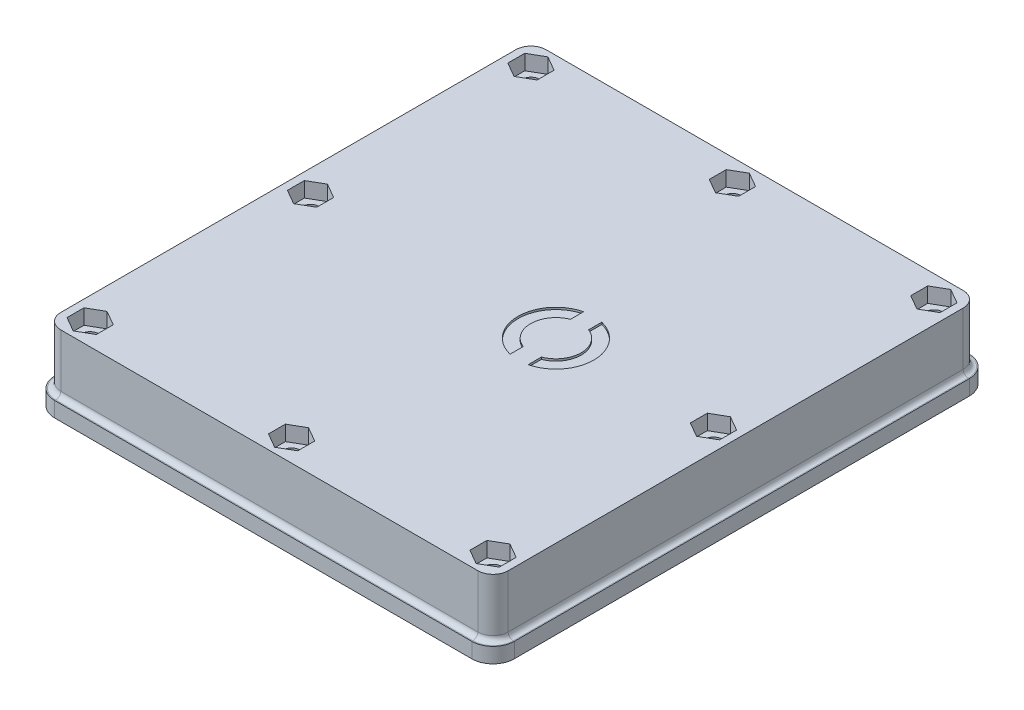
SolidWorks part; units mm, degrees
ref_plane "Спереди" through (0, 0, 0) normal (0, 0, 1) x (1, 0, 0)
ref_plane "Сверху" through (0, 0, 0) normal (0, 1, 0) x (1, 0, 0)
ref_plane "Справа" through (0, 0, 0) normal (1, 0, 0) x (0, 0, -1)
sketch "Эскиз1" plane through (0, 0, 0) normal (0, 1, 0) x (1, 0, 0)
  line L0 (-41.9993, -47.5511) -> (40.5007, -47.5511)
  line L1 (43.5007, 45.4489) -> (43.5007, -44.5511)
  line L2 (-44.9993, 45.4489) -> (-44.9993, -44.5511)
  line L3 (-41.9993, 48.4489) -> (40.5007, 48.4489)
  line L4 (-17.4039, -31.5511) -> (-17.4039, -29.173)
  line L5 (-17.4039, -29.173) -> (-15.9993, -29.173)
  line L6 (-15.9993, 40.4489) -> (38.0007, 40.4489)
  line L7 (38.0007, 10.4489) -> (38.0007, 40.4489)
  line L8 (35.5007, 10.4489) -> (38.0007, 10.4489)
  line L9 (35.5007, 10.4489) -> (35.5007, -29.0511)
  line L10 (35.5007, -39.5511) -> (35.5007, -30.0511)
  line L11 (27.5007, -39.5511) -> (35.5007, -39.5511)
  line L12 (27.5007, -30.0511) -> (27.5007, -39.5511)
  line L13 (21.0007, -30.0511) -> (27.5007, -30.0511)
  line L14 (-15.9993, -29.173) -> (-15.9993, -31.5511)
  line L15 (-15.9993, -31.5511) -> (21.0007, -31.5511)
  line L17 (-17.4039, 40.4489) -> (-17.4039, 31.327)
  line L18 (-17.4039, 40.4489) -> (-17.4039, 41.327)
  line L19 (-17.4039, 31.327) -> (-15.9993, 31.327)
  line L20 (-15.9993, 31.327) -> (-15.9993, 40.4489)
  line L25 (21.0007, -31.5511) -> (21.0007, -30.0511)
  line L26 (35.5007, -29.0511) -> (35.5007, -30.0511)
  line L27 (-36.6539, 1.077) -> (-17.6539, 1.077) construction
  line L29 (-17.4039, -39.173) -> (-36.9039, -39.173)
  line L30 (-17.4039, -39.173) -> (-17.4039, -31.5511)
  line L31 (-17.4039, 41.327) -> (-36.9039, 41.327)
  line L32 (-36.9039, -39.173) -> (-36.9039, 41.327)
  line L33 (-17.4039, -39.173) -> (-36.9039, 41.327) construction
  line L34 (-17.4039, 41.327) -> (-36.9039, -39.173) construction
  circle A0 centre (-40.5993, 0.4489) radius 1.7
  arc A1 (-44.9993, -44.5511) -> (-41.9993, -47.5511) centre (-41.9993, -44.5511) ccw
  circle A2 centre (-40.5993, -43.1511) radius 1.7
  circle A3 centre (-0.7493, -43.1511) radius 1.7
  arc A4 (40.5007, -47.5511) -> (43.5007, -44.5511) centre (40.5007, -44.5511) ccw
  circle A5 centre (39.1007, -43.1511) radius 1.7
  circle A6 centre (39.1007, 0.4489) radius 1.7
  arc A7 (43.5007, 45.4489) -> (40.5007, 48.4489) centre (40.5007, 45.4489) ccw
  circle A8 centre (39.1007, 44.0489) radius 1.7
  circle A9 centre (-0.7493, 44.0489) radius 1.7
  circle A10 centre (-40.5993, 44.0489) radius 1.7
  arc A11 (-41.9993, 48.4489) -> (-44.9993, 45.4489) centre (-41.9993, 45.4489) ccw
  point P20 (-27.1539, 1.077)
  point P60 (-27.1539, 41.327)
  point P61 (-27.1539, -39.173)
  dimension "D3" = 10
  dimension "D1" = 19.5
  dimension "D2" = 80.5
  dimension "D4" = 10
extrude "Бобышка-Вытянуть1" add sketch "Эскиз1" along normal blind 10
sketch "Эскиз2" plane through (0, 10, 0) normal (0, 1, 0) x (1, 0, 0)
  line L0 (43.5007, 45.4489) -> (43.5007, -44.5511) construction
  line L1 (-41.9993, -47.5511) -> (40.5007, -47.5511) construction
  line L2 (-44.9993, 45.4489) -> (-44.9993, -44.5511) construction
  line L3 (-41.9993, 48.4489) -> (40.5007, 48.4489) construction
  line L4 (43.5007, 45.4489) -> (43.5007, -44.5511)
  line L5 (-41.9993, -47.5511) -> (40.5007, -47.5511)
  line L6 (-44.9993, 45.4489) -> (-44.9993, -44.5511)
  line L7 (-41.9993, 48.4489) -> (40.5007, 48.4489)
  arc A0 (43.5007, 45.4489) -> (40.5007, 48.4489) centre (40.5007, 45.4489) ccw construction
  arc A1 (40.5007, -47.5511) -> (43.5007, -44.5511) centre (40.5007, -44.5511) ccw construction
  arc A2 (-44.9993, -44.5511) -> (-41.9993, -47.5511) centre (-41.9993, -44.5511) ccw construction
  arc A3 (-41.9993, 48.4489) -> (-44.9993, 45.4489) centre (-41.9993, 45.4489) ccw construction
  arc A4 (43.5007, 45.4489) -> (40.5007, 48.4489) centre (40.5007, 45.4489) ccw
  arc A5 (40.5007, -47.5511) -> (43.5007, -44.5511) centre (40.5007, -44.5511) ccw
  arc A6 (-44.9993, -44.5511) -> (-41.9993, -47.5511) centre (-41.9993, -44.5511) ccw
  arc A7 (-41.9993, 48.4489) -> (-44.9993, 45.4489) centre (-41.9993, 45.4489) ccw
  circle A8 centre (39.1007, 0.4489) radius 1.7 construction
  circle A9 centre (39.1007, -43.1511) radius 1.7 construction
  circle A10 centre (-0.7493, -43.1511) radius 1.7 construction
  circle A11 centre (-40.5993, -43.1511) radius 1.7 construction
  circle A12 centre (-40.5993, 0.4489) radius 1.7 construction
  circle A13 centre (39.1007, 44.0489) radius 1.7 construction
  circle A14 centre (-0.7493, 44.0489) radius 1.7 construction
  circle A15 centre (-40.5993, 44.0489) radius 1.7 construction
  circle A16 centre (39.1007, 0.4489) radius 1.7
  circle A17 centre (39.1007, -43.1511) radius 1.7
  circle A18 centre (-0.7493, -43.1511) radius 1.7
  circle A19 centre (-40.5993, -43.1511) radius 1.7
  circle A20 centre (-40.5993, 0.4489) radius 1.7
  circle A21 centre (39.1007, 44.0489) radius 1.7
  circle A22 centre (-0.7493, 44.0489) radius 1.7
  circle A23 centre (-40.5993, 44.0489) radius 1.7
extrude "Бобышка-Вытянуть2" add sketch "Эскиз2" along normal blind 2.5
fillet "Скругление1" radius 9.5 1 edges at (-36.9039, 10, -1.077)
fillet "Скругление2" radius 9.5 1 edges at (-17.4039, 10, 34.173)
sketch "Эскиз3" plane through (0, 10, 0) normal (0, -1, 0) x (1, 0, 0)
  line L0 (39.1007, -0.4489) -> (-40.5993, -0.4489) construction
  circle A0 centre (9.1007, -2.4489) radius 3
  circle A1 centre (9.1007, -2.4489) radius 5
  point P4 (9.1007, -2.4489)
  dimension "D3" = 6
  dimension "D4" = 10
  dimension "D1" = 2
  dimension "D2" = 30
fillet "Скругление3" radius 9.5 1 edges at (-17.4039, 10, -36.327)
extrude "Бобышка-Вытянуть3" add sketch "Эскиз3" along normal blind 3
sketch "Эскиз4" plane through (0, 12.5, 0) normal (0, 1, 0) x (1, 0, 0)
  line L0 (8.3881, 12.0563) -> (8.3881, -12.8952) construction
  line L1 (6.5927, 7.2819) -> (6.5927, 4.6666)
  line L2 (10.1834, 7.2819) -> (10.1834, 4.6666)
  line L3 (6.5927, -4.6666) -> (6.5927, -7.2819)
  line L4 (10.1834, -4.6666) -> (10.1834, -7.2819)
  arc A0 (6.5927, 4.6666) -> (6.5927, -4.6666) centre (8.3881, 0) ccw
  arc A1 (6.5927, 7.2819) -> (6.5927, -7.2819) centre (8.3881, 0) ccw
  arc A2 (10.1834, -4.6666) -> (10.1834, 4.6666) centre (8.3881, 0) ccw
  arc A3 (10.1834, -7.2819) -> (10.1834, 7.2819) centre (8.3881, 0) ccw
  dimension "D1" = 10
  dimension "D2" = 15
extrude "Вырез-Вытянуть1" cut sketch "Эскиз4" against normal blind 0.4
sketch "Эскиз5" plane through (0, 12.5, 0) normal (0, 1, 0) x (1, 0, 0)
  line L0 (43.5007, 0.4489) -> (-44.9993, 0.4489) construction
  line L1 (-40.5993, 40.7002) -> (-37.6993, 42.3746)
  line L2 (-37.6993, 42.3746) -> (-37.6993, 45.7232)
  line L3 (-37.6993, 45.7232) -> (-40.5993, 47.3975)
  line L4 (-40.5993, 47.3975) -> (-43.4993, 45.7232)
  line L5 (-43.4993, 45.7232) -> (-43.4993, 42.3746)
  line L6 (-43.4993, 42.3746) -> (-40.5993, 40.7002)
  line L7 (-0.7493, 40.7002) -> (2.1507, 42.3746)
  line L8 (2.1507, 42.3746) -> (2.1507, 45.7232)
  line L9 (2.1507, 45.7232) -> (-0.7493, 47.3975)
  line L10 (-0.7493, 47.3975) -> (-3.6493, 45.7232)
  line L11 (-3.6493, 45.7232) -> (-3.6493, 42.3746)
  line L12 (-3.6493, 42.3746) -> (-0.7493, 40.7002)
  line L13 (-40.5993, 3.7975) -> (-43.4993, 2.1232)
  line L14 (-43.4993, 2.1232) -> (-43.4993, -1.2254)
  line L15 (-43.4993, -1.2254) -> (-40.5993, -2.8998)
  line L16 (-40.5993, -2.8998) -> (-37.6993, -1.2254)
  line L17 (-37.6993, -1.2254) -> (-37.6993, 2.1232)
  line L18 (-37.6993, 2.1232) -> (-40.5993, 3.7975)
  line L19 (43.5007, -44.5511) -> (43.5007, 45.4489) construction
  line L20 (-44.9993, 45.4489) -> (-44.9993, -44.5511) construction
  line L21 (-0.7493, 48.4489) -> (-0.7493, -47.5511) construction
  line L22 (40.5007, 48.4489) -> (-41.9993, 48.4489) construction
  line L23 (-41.9993, -47.5511) -> (40.5007, -47.5511) construction
  line L24 (36.2007, 2.1232) -> (39.1007, 3.7975)
  line L25 (36.2007, -1.2254) -> (36.2007, 2.1232)
  line L26 (39.1007, -2.8998) -> (36.2007, -1.2254)
  line L27 (42.0007, -1.2254) -> (39.1007, -2.8998)
  line L28 (42.0007, 2.1232) -> (42.0007, -1.2254)
  line L29 (39.1007, 3.7975) -> (42.0007, 2.1232)
  line L30 (42.0007, 42.3746) -> (39.1007, 40.7002)
  line L31 (42.0007, 45.7232) -> (42.0007, 42.3746)
  line L32 (39.1007, 47.3975) -> (42.0007, 45.7232)
  line L33 (36.2007, 45.7232) -> (39.1007, 47.3975)
  line L34 (36.2007, 42.3746) -> (36.2007, 45.7232)
  line L35 (39.1007, 40.7002) -> (36.2007, 42.3746)
  line L36 (39.1007, -39.8025) -> (36.2007, -41.4768)
  line L37 (36.2007, -41.4768) -> (36.2007, -44.8254)
  line L38 (36.2007, -44.8254) -> (39.1007, -46.4998)
  line L39 (39.1007, -46.4998) -> (42.0007, -44.8254)
  line L40 (42.0007, -44.8254) -> (42.0007, -41.4768)
  line L41 (42.0007, -41.4768) -> (39.1007, -39.8025)
  line L42 (-3.6493, -41.4768) -> (-0.7493, -39.8025)
  line L43 (-3.6493, -44.8254) -> (-3.6493, -41.4768)
  line L44 (-0.7493, -46.4998) -> (-3.6493, -44.8254)
  line L45 (2.1507, -44.8254) -> (-0.7493, -46.4998)
  line L46 (2.1507, -41.4768) -> (2.1507, -44.8254)
  line L47 (-0.7493, -39.8025) -> (2.1507, -41.4768)
  line L48 (-43.4993, -41.4768) -> (-40.5993, -39.8025)
  line L49 (-43.4993, -44.8254) -> (-43.4993, -41.4768)
  line L50 (-40.5993, -46.4998) -> (-43.4993, -44.8254)
  line L51 (-37.6993, -44.8254) -> (-40.5993, -46.4998)
  line L52 (-37.6993, -41.4768) -> (-37.6993, -44.8254)
  line L53 (-40.5993, -39.8025) -> (-37.6993, -41.4768)
  circle A0 centre (-40.5993, 44.0489) radius 2.9 construction
  circle A1 centre (-0.7493, 44.0489) radius 2.9 construction
  circle A2 centre (-40.5993, 0.4489) radius 2.9 construction
  circle A3 centre (39.1007, 0.4489) radius 2.9 construction
  circle A4 centre (39.1007, 44.0489) radius 2.9 construction
  circle A5 centre (39.1007, -43.1511) radius 2.9 construction
  circle A6 centre (-0.7493, -43.1511) radius 2.9 construction
  circle A7 centre (-40.5993, -43.1511) radius 2.9 construction
extrude "Вырез-Вытянуть2" cut sketch "Эскиз5" against normal blind 3
sketch "Эскиз6" plane through (0, 10, 0) normal (0, -1, 0) x (1, 0, 0)
  line L0 (27.5007, 30.0511) -> (35.5007, 30.0511)
  line L1 (35.5007, -10.4489) -> (35.5007, 39.5511) construction
  line L2 (35.5007, 30.0511) -> (35.5007, 39.5511)
  line L3 (35.5007, 39.5511) -> (27.5007, 39.5511)
  line L4 (27.5007, 39.5511) -> (27.5007, 30.0511)
  line L5 (35.5007, -10.4489) -> (35.5007, -40.4489)
  line L6 (-15.9993, -40.4489) -> (38.0007, -40.4489) construction
  line L7 (35.5007, -40.4489) -> (38.0007, -40.4489)
  line L8 (38.0007, -40.4489) -> (38.0007, -10.4489)
  line L9 (38.0007, -10.4489) -> (35.5007, -10.4489)
extrude "Бобышка-Вытянуть4" add sketch "Эскиз6" along normal blind 5
sketch "Эскиз8" plane through (0, 10, 0) normal (0, -1, 0) x (1, 0, 0)
  line L0 (35.5007, -5.2489) -> (35.5007, 4.3511)
  line L1 (35.5007, -10.4489) -> (35.5007, 39.5511) construction
  line L2 (35.5007, -40.4489) -> (35.5007, 30.0511) construction
  line L3 (-5.5493, -40.4489) -> (4.0507, -40.4489)
  line L4 (-15.9993, -40.4489) -> (35.5007, -40.4489) construction
  arc A0 (4.0507, -40.4489) -> (-5.5493, -40.4489) centre (-0.7493, -44.0489) ccw
  arc A1 (35.5007, 4.3511) -> (35.5007, -5.2489) centre (39.1007, -0.4489) ccw
  dimension "D1" = 12
  dimension "D2" = 12
extrude "Бобышка-Вытянуть5" add sketch "Эскиз8" along normal blind 2
sketch "Эскиз9" plane through (0, 0, 0) normal (0, -1, 0) x (1, 0, 0)
  line L0 (-41.9993, -48.4489) -> (40.5007, -48.4489) construction
  line L1 (43.5007, -45.4489) -> (43.5007, 44.5511) construction
  line L2 (-44.9993, -45.4489) -> (-44.9993, 44.5511) construction
  line L3 (-41.9993, 47.5511) -> (40.5007, 47.5511) construction
  line L4 (-41.9993, -48.4489) -> (40.5007, -48.4489)
  line L5 (43.5007, -45.4489) -> (43.5007, 44.5511)
  line L6 (-44.9993, -45.4489) -> (-44.9993, 44.5511)
  line L7 (-41.9993, 47.5511) -> (40.5007, 47.5511)
  arc A0 (-44.9993, -45.4489) -> (-41.9993, -48.4489) centre (-41.9993, -45.4489) ccw construction
  arc A1 (40.5007, -48.4489) -> (43.5007, -45.4489) centre (40.5007, -45.4489) ccw construction
  arc A2 (43.5007, 44.5511) -> (40.5007, 47.5511) centre (40.5007, 44.5511) ccw construction
  arc A3 (-41.9993, 47.5511) -> (-44.9993, 44.5511) centre (-41.9993, 44.5511) ccw construction
  arc A4 (-44.9993, -45.4489) -> (-41.9993, -48.4489) centre (-41.9993, -45.4489) ccw
  arc A5 (40.5007, -48.4489) -> (43.5007, -45.4489) centre (40.5007, -45.4489) ccw
  arc A6 (43.5007, 44.5511) -> (40.5007, 47.5511) centre (40.5007, 44.5511) ccw
  arc A7 (-41.9993, 47.5511) -> (-44.9993, 44.5511) centre (-41.9993, 44.5511) ccw
extrude "Вытянуть-Тонкостенный1" add sketch "Эскиз9" along normal blind 2 thin thin type one direction reverse wall 1.3
sketch "Эскиз11" plane through (0, -2, 0) normal (0, -1, 0) x (1, 0, 0)
  line L0 (40.5007, 46.2511) -> (-41.9993, 46.2511) construction
  line L1 (42.2007, -45.4489) -> (42.2007, 44.5511) construction
  line L2 (-41.9993, -47.1489) -> (40.5007, -47.1489) construction
  line L3 (-43.6993, 44.5511) -> (-43.6993, -45.4489) construction
  line L4 (40.5007, 46.2511) -> (-41.9993, 46.2511)
  line L5 (42.2007, -45.4489) -> (42.2007, 44.5511)
  line L6 (-41.9993, -47.1489) -> (40.5007, -47.1489)
  line L7 (-43.6993, 44.5511) -> (-43.6993, -45.4489)
  arc A0 (-41.9993, 46.2511) -> (-43.6993, 44.5511) centre (-41.9993, 44.5511) ccw construction
  arc A1 (42.2007, 44.5511) -> (40.5007, 46.2511) centre (40.5007, 44.5511) ccw construction
  arc A2 (40.5007, -47.1489) -> (42.2007, -45.4489) centre (40.5007, -45.4489) ccw construction
  arc A3 (-43.6993, -45.4489) -> (-41.9993, -47.1489) centre (-41.9993, -45.4489) ccw construction
  arc A4 (-41.9993, 46.2511) -> (-43.6993, 44.5511) centre (-41.9993, 44.5511) ccw
  arc A5 (42.2007, 44.5511) -> (40.5007, 46.2511) centre (40.5007, 44.5511) ccw
  arc A6 (40.5007, -47.1489) -> (42.2007, -45.4489) centre (40.5007, -45.4489) ccw
  arc A7 (-43.6993, -45.4489) -> (-41.9993, -47.1489) centre (-41.9993, -45.4489) ccw
extrude "Вытянуть-Тонкостенный3" add sketch "Эскиз11" against normal blind 3 thin
fillet "Скругление4" radius 1 8 edges at (42.6221, 1, 46.6725) (-0.7493, 1, 47.5511) (-44.1206, 1, 46.6725) (-44.9993, 1, -0.4489) (-44.1206, 1, -47.5702) (-0.7493, 1, -48.4489) (42.6221, 1, -47.5702) (43.5007, 1, -0.4489)
